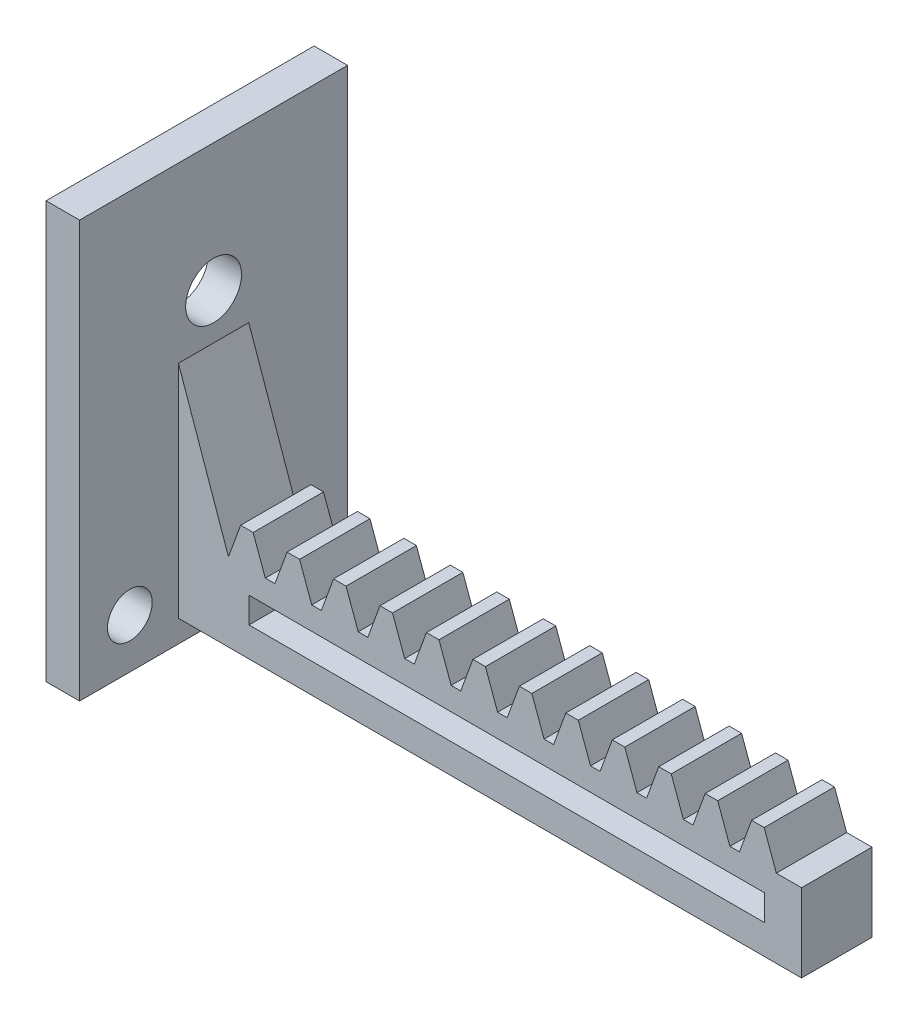
SolidWorks part; units mm, degrees
ref_plane "Front Plane" through (0, 0, 0) normal (0, 0, 1) x (1, 0, 0)
ref_plane "Top Plane" through (0, 0, 0) normal (0, 1, 0) x (1, 0, 0)
ref_plane "Right Plane" through (0, 0, 0) normal (1, 0, 0) x (0, 0, -1)
sketch "Sketch1" plane through (0, 0, 0) normal (0, 0, 1) x (1, 0, 0)
  line L1 (-27.9, -3.5) -> (27.9, -3.5)
  line L2 (-27.9, -3.5) -> (-27.9, 3.5)
  line L3 (-27.9, 3.5) -> (27.9, 3.5)
  line L4 (27.9, -3.5) -> (27.9, 3.5)
  line L5 (-27.9, -3.5) -> (27.9, 3.5) construction
  line L6 (-27.9, 3.5) -> (27.9, -3.5) construction
  point P0 (0, 0)
  dimension "D1" = 7
  dimension "D2" = 55.8
extrude "Boss-Extrude2" add sketch "Sketch1" along normal blind 6.3
sketch "Sketch2" plane through (0, 0, 6.3) normal (0, 0, 1) x (1, 0, 0)
  line L0 (-27.9, 0) -> (-21.58, 0) construction
  line L1 (27.9, -3.5) -> (24.6, -3.5)
  line L5 (27.9, 3.5) -> (24.6, 3.5)
  line L9 (-27.9, 3.5) -> (-27.9, -3.5) construction
  line L10 (-27.9, 3.5) -> (-23.7872, 3.5) construction
  line L11 (27.9, 3.5) -> (-27.9, 3.5) construction
  line L12 (-23.7872, 3.5) -> (-21.4701, 3.5) construction
  line L14 (24.6, 1.45) -> (-21.58, 1.45)
  line L15 (24.6, 1.45) -> (24.6, -0.86)
  line L16 (24.6, -0.86) -> (-21.58, -0.86)
  line L17 (-21.58, 1.45) -> (-21.58, -0.86)
  dimension "D2" = 2.05
  dimension "D3" = 2.64
  dimension "D5" = 6.32
extrude "Cut-Extrude1" cut sketch "Sketch2" against normal blind 6.3 contours L14 L17 L16 L15
sketch "Sketch3" plane through (0, 0, 6.3) normal (0, 0, 1) x (1, 0, 0)
  line L0 (-27.9, 3.5) -> (-23.42, 3.5) construction
  line L1 (-27.9, 3.5) -> (-27.9, -3.5) construction
  line L2 (27.9, 3.5) -> (-27.9, 3.5) construction
  line L3 (-23.42, 3.5) -> (-22.331, 3.5) construction
  line L4 (-22.331, 3.5) -> (-22.331, 6.494) construction
  line L5 (-23.42, 3.5) -> (-22.331, 6.494)
  line L6 (-22.331, 6.494) -> (-21.209, 6.494)
  line L7 (-21.77, 6.494) -> (-21.77, 6.2621) construction
  line L8 (-20.12, 3.5) -> (-21.209, 6.494)
  line L9 (-23.42, 3.5) -> (-20.12, 3.5)
  line L10 (-20.0245, 3.5) -> (-19.5845, 3.5) construction
  line L11 (-19.26, 3.5) -> (-15.96, 3.5)
  line L12 (-15.96, 3.5) -> (-17.049, 6.494)
  line L13 (-18.171, 6.494) -> (-17.049, 6.494)
  line L14 (-19.26, 3.5) -> (-18.171, 6.494)
  line L15 (-15.1, 3.5) -> (-11.8, 3.5)
  line L16 (-11.8, 3.5) -> (-12.889, 6.494)
  line L17 (-14.011, 6.494) -> (-12.889, 6.494)
  line L18 (-15.1, 3.5) -> (-14.011, 6.494)
  line L19 (-10.94, 3.5) -> (-7.64, 3.5)
  line L20 (-7.64, 3.5) -> (-8.729, 6.494)
  line L21 (-9.851, 6.494) -> (-8.729, 6.494)
  line L22 (-10.94, 3.5) -> (-9.851, 6.494)
  line L23 (-6.78, 3.5) -> (-3.48, 3.5)
  line L24 (-3.48, 3.5) -> (-4.569, 6.494)
  line L25 (-5.691, 6.494) -> (-4.569, 6.494)
  line L26 (-6.78, 3.5) -> (-5.691, 6.494)
  line L27 (-2.62, 3.5) -> (0.68, 3.5)
  line L28 (0.68, 3.5) -> (-0.409, 6.494)
  line L29 (-1.531, 6.494) -> (-0.409, 6.494)
  line L30 (-2.62, 3.5) -> (-1.531, 6.494)
  line L31 (1.54, 3.5) -> (4.84, 3.5)
  line L32 (4.84, 3.5) -> (3.751, 6.494)
  line L33 (2.629, 6.494) -> (3.751, 6.494)
  line L34 (1.54, 3.5) -> (2.629, 6.494)
  line L35 (5.7, 3.5) -> (9, 3.5)
  line L36 (9, 3.5) -> (7.911, 6.494)
  line L37 (6.789, 6.494) -> (7.911, 6.494)
  line L38 (5.7, 3.5) -> (6.789, 6.494)
  line L39 (9.86, 3.5) -> (13.16, 3.5)
  line L40 (13.16, 3.5) -> (12.071, 6.494)
  line L41 (10.949, 6.494) -> (12.071, 6.494)
  line L42 (9.86, 3.5) -> (10.949, 6.494)
  line L43 (14.02, 3.5) -> (17.32, 3.5)
  line L44 (17.32, 3.5) -> (16.231, 6.494)
  line L45 (15.109, 6.494) -> (16.231, 6.494)
  line L46 (14.02, 3.5) -> (15.109, 6.494)
  line L47 (18.18, 3.5) -> (21.48, 3.5)
  line L48 (21.48, 3.5) -> (20.391, 6.494)
  line L49 (19.269, 6.494) -> (20.391, 6.494)
  line L50 (18.18, 3.5) -> (19.269, 6.494)
  line L51 (22.34, 3.5) -> (25.64, 3.5)
  line L52 (25.64, 3.5) -> (24.551, 6.494)
  line L53 (23.429, 6.494) -> (24.551, 6.494)
  line L54 (22.34, 3.5) -> (23.429, 6.494)
  dimension "D1" = 4.48
  dimension "D2" = 1.089
  dimension "D3" = 2.994
  dimension "D4" = 1.122
  dimension "D5" = 0.44
  dimension "D6" = 12
extrude "Boss-Extrude3" add sketch "Sketch3" against normal blind 6.3
ref_plane "Plane1" through (0, -3.5, 0) normal (0, -1, 0) x (-1, 0, 0)
sketch "Sketch5" plane through (0, -3.5, 0) normal (0, -1, 0) x (-1, 0, 0)
  line L0 (27.9, -3.15) -> (31.9, -3.15) construction
  line L1 (27.9, -6.3) -> (27.9, 0) construction
  line L2 (27.9, -15.15) -> (27.9, 8.85)
  line L3 (27.9, 8.85) -> (30.9, 8.85)
  line L4 (30.9, 8.85) -> (30.9, -15.15)
  line L6 (27.9, -15.15) -> (30.9, -15.15)
  dimension "D1" = 12
  dimension "D2" = 3
extrude "Boss-Extrude4" add sketch "Sketch5" against normal blind 35.3
sketch "Sketch6" plane through (-27.9, 0, 0) normal (1, 0, 0) x (0, 0, -1)
  line L0 (-15.15, 1.34) -> (8.85, 1.34) construction
  line L1 (-15.15, 31.8) -> (-15.15, -3.5) construction
  line L2 (8.85, 31.8) -> (8.85, -3.5) construction
  line L3 (8.85, 1.34) -> (-3.15, 1.34) construction
  line L4 (-3.15, 1.34) -> (-3.15, -4.5616) construction
  line L5 (-6.3, -3.5) -> (-15.15, -3.5) construction
  line L6 (4.25, 1.34) -> (4.25, -3.5) construction
  line L7 (8.85, -3.5) -> (0, -3.5) construction
  line L8 (4.25, 1.34) -> (8.85, 1.34) construction
  line L9 (8.85, 1.34) -> (6.55, 1.34) construction
  line L10 (6.55, 1.34) -> (6.55, 1.0051) construction
  line L11 (-3.15, 1.34) -> (-3.15, 20.34) construction
  circle A0 centre (4.35, -1.08) radius 2
  circle A1 centre (-10.65, -1.08) radius 2
  circle A2 centre (-3.15, 20.34) radius 2.5
  point P22 (0, 0)
  point P23 (0, 0)
  dimension "D3" = 4
  dimension "D5" = 5
  dimension "D1" = 4.84
  dimension "D2" = 4.6
  dimension "D4" = 19
  dimension "D6" = 15
extrude "Cut-Extrude2" cut sketch "Sketch6" against normal blind 40
sketch "Sketch7" plane through (0, 0, 0) normal (0, 0, -1) x (-1, 0, 0)
  line L0 (23.42, 3.5) -> (27.9, 16.2748)
  line L1 (23.42, 3.5) -> (27.9, 3.5) construction
  line L2 (27.9, 31.8) -> (27.9, -3.5) construction
  line L3 (27.9, 16.2748) -> (27.9, 8.8092)
  line L6 (23.42, 3.5) -> (27.9, 3.5)
  line L7 (27.9, 3.5) -> (27.9, 8.8092)
extrude "Boss-Extrude5" add sketch "Sketch7" against normal blind 6.3
sketch "Sketch8" plane through (0, -3.5, 0) normal (0, -1, 0) x (1, 0, 0)
  line L0 (-30.9, -8.85) -> (-27.9, -8.85) construction
  line L1 (-30.9, -8.85) -> (-27.9, -8.85)
  line L2 (-30.9, -8.85) -> (-30.9, 15.15)
  line L3 (-30.9, 15.15) -> (-27.9, 15.15)
  line L4 (-27.9, -8.85) -> (-27.9, 15.15)
  line L5 (-30.9, 15.15) -> (-30.9, -8.85) construction
  line L6 (-27.9, 15.15) -> (-30.9, 15.15) construction
extrude "Boss-Extrude6" add sketch "Sketch8" along normal blind 2
